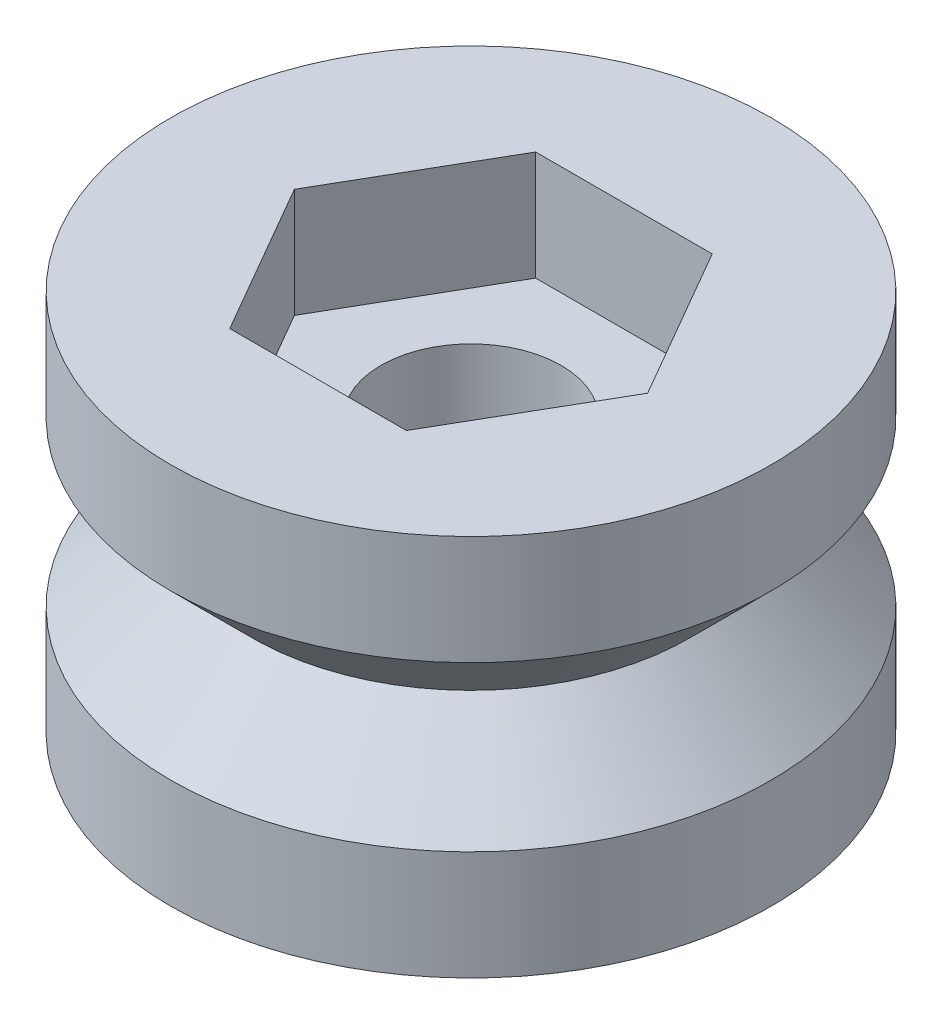
SolidWorks part; units mm, degrees
ref_plane "Plano frontal" through (0, 0, 0) normal (0, 0, 1) x (1, 0, 0)
ref_plane "Plano superior" through (0, 0, 0) normal (0, 1, 0) x (1, 0, 0)
ref_plane "Plano direito" through (0, 0, 0) normal (1, 0, 0) x (0, 0, -1)
sketch "Esboço1" plane through (0, 0, 0) normal (0, 0, 1) x (1, 0, 0)
  line L0 (1.65, 0) -> (5.5, 0)
  line L1 (5.5, 0) -> (5.5, 2)
  line L2 (5.5, 2) -> (4, 3.5)
  line L3 (4, 3.5) -> (5.5, 5)
  line L4 (5.5, 5) -> (5.5, 7)
  line L5 (5.5, 7) -> (1.65, 7)
  line L6 (1.65, 7) -> (1.65, 0)
  line L7 (0, 0) -> (0, 5.4299) construction
  point P10 (4.1298, 0.7403)
  dimension "D1" = 7
  dimension "D2" = 3.3
  dimension "D3" = 2
  dimension "D4" = 8
revolve "Revolução1" add sketch "Esboço1" angle 360 about L7
sketch "Esboço2" plane through (0, 7, 0) normal (0, 1, 0) x (1, 0, 0)
  line L1 (3.2332, 0) -> (1.6166, 2.8)
  line L2 (1.6166, 2.8) -> (-1.6166, 2.8)
  line L3 (-1.6166, 2.8) -> (-3.2332, 0)
  line L4 (-3.2332, 0) -> (-1.6166, -2.8)
  line L5 (-1.6166, -2.8) -> (1.6166, -2.8)
  line L6 (1.6166, -2.8) -> (3.2332, 0)
  circle A0 centre (0, 0) radius 2.8 construction
  dimension "D1" = 5.6
extrude "Corte-extrusão1" cut sketch "Esboço2" against normal blind 2
